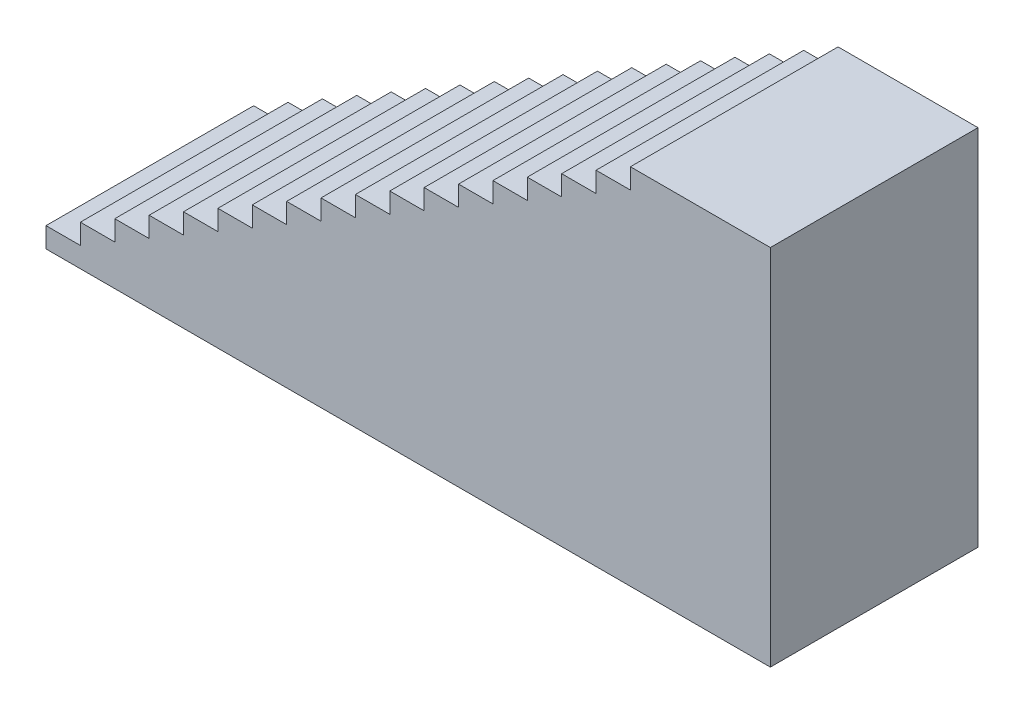
SolidWorks part; units mm, degrees
ref_plane "Front Plane" through (0, 0, 0) normal (0, 0, 1) x (1, 0, 0)
ref_plane "Top Plane" through (0, 0, 0) normal (0, 1, 0) x (1, 0, 0)
ref_plane "Right Plane" through (0, 0, 0) normal (1, 0, 0) x (0, 0, -1)
sketch "Sketch1" plane through (0, 0, 0) normal (0, 0, 1) x (1, 0, 0)
  line L1 (-855.5229, 508.7368) -> (815.0351, 508.7368)
  line L2 (-855.5229, 508.7368) -> (-855.5229, -291.3632)
  line L3 (-855.5229, -291.3632) -> (815.0351, -291.3632)
  line L4 (815.0351, 508.7368) -> (815.0351, -291.3632)
  dimension "D1" = 1670.558
  dimension "D2" = 800.1
extrude "Boss-Extrude1" add sketch "Sketch1" along normal blind 457.2
sketch "Sketch2" plane through (0, 0, 457.2) normal (0, 0, 1) x (1, 0, 0)
  line L0 (815.0351, -291.3632) -> (815.0351, 508.7368) construction
  line L3 (815.0351, 508.7368) -> (-855.5229, 508.7368) construction
  line L4 (506.9331, 508.7368) -> (506.9331, 464.2868)
  line L5 (506.9331, 464.2868) -> (431.2411, 464.2868)
  line L6 (431.2411, 464.2868) -> (431.2411, 419.8368)
  line L7 (431.2411, 419.8368) -> (355.5491, 419.8368)
  line L8 (355.5491, 419.8368) -> (355.5491, 375.3868)
  line L9 (355.5491, 375.3868) -> (279.8571, 375.3868)
  line L10 (279.8571, 375.3868) -> (279.8571, 330.9368)
  line L11 (279.8571, 330.9368) -> (204.1651, 330.9368)
  line L12 (204.1651, 330.9368) -> (204.1651, 286.4868)
  line L13 (204.1651, 286.4868) -> (128.4731, 286.4868)
  line L14 (128.4731, 286.4868) -> (128.4731, 242.0368)
  line L15 (128.4731, 242.0368) -> (52.7811, 242.0368)
  line L16 (52.7811, 242.0368) -> (52.7811, 197.5868)
  line L17 (52.7811, 197.5868) -> (-22.9109, 197.5868)
  line L18 (-22.9109, 197.5868) -> (-22.9109, 153.1368)
  line L19 (-22.9109, 153.1368) -> (-98.6029, 153.1368)
  line L20 (-98.6029, 153.1368) -> (-98.6029, 108.6868)
  line L21 (-98.6029, 108.6868) -> (-174.2949, 108.6868)
  line L22 (-174.2949, 108.6868) -> (-174.2949, 64.2368)
  line L23 (-174.2949, 64.2368) -> (-249.9869, 64.2368)
  line L24 (-249.9869, 64.2368) -> (-249.9869, 19.7868)
  line L25 (-249.9869, 19.7868) -> (-325.6789, 19.7868)
  line L26 (-325.6789, 19.7868) -> (-325.6789, -24.6632)
  line L27 (-325.6789, -24.6632) -> (-401.3709, -24.6632)
  line L28 (-401.3709, -24.6632) -> (-401.3709, -69.1132)
  line L29 (-401.3709, -69.1132) -> (-477.0629, -69.1132)
  line L30 (-477.0629, -69.1132) -> (-477.0629, -113.5632)
  line L31 (-477.0629, -113.5632) -> (-552.7549, -113.5632)
  line L32 (-552.7549, -113.5632) -> (-552.7549, -158.0132)
  line L33 (-552.7549, -158.0132) -> (-628.4469, -158.0132)
  line L34 (-628.4469, -158.0132) -> (-628.4469, -202.4632)
  line L35 (-628.4469, -202.4632) -> (-704.1389, -202.4632)
  line L36 (-704.1389, -202.4632) -> (-704.1389, -246.9132)
  line L37 (-704.1389, -246.9132) -> (-779.8309, -246.9132)
  line L38 (-779.8309, -246.9132) -> (-779.8309, -291.3632)
  line L39 (-779.8309, -291.3632) -> (-855.5229, -291.3632)
  line L40 (-855.5229, -291.3632) -> (-855.5229, 508.7368)
  line L41 (-855.5229, 508.7368) -> (506.9331, 508.7368)
  dimension "D3" = 75.692
  dimension "D4" = 75.692
  dimension "D5" = 75.692
  dimension "D6" = 44.45
  dimension "D7" = 44.45
  dimension "D8" = 75.692
  dimension "D9" = 44.45
  dimension "D10" = 44.45
  dimension "D11" = 44.45
  dimension "D12" = 75.692
  dimension "D13" = 75.692
  dimension "D14" = 75.692
  dimension "D15" = 75.692
  dimension "D16" = 75.692
  dimension "D17" = 75.692
  dimension "D18" = 75.692
  dimension "D19" = 75.692
  dimension "D20" = 75.692
  dimension "D21" = 75.692
  dimension "D22" = 75.692
  dimension "D23" = 75.692
  dimension "D24" = 75.692
  dimension "D25" = 44.45
  dimension "D26" = 44.45
  dimension "D27" = 44.45
  dimension "D28" = 44.45
  dimension "D29" = 44.45
  dimension "D30" = 44.45
  dimension "D31" = 44.45
  dimension "D32" = 44.45
  dimension "D33" = 44.45
  dimension "D34" = 44.45
  dimension "D35" = 44.45
  dimension "D36" = 44.45
  dimension "D37" = 308.102
extrude "Cut-Extrude1" cut sketch "Sketch2" against normal blind 457.2 contours L27 L28 L29 L30 L31 L32 L33 L34 L35 L36 L37 L38 L39 L40 L41 L4 L5 L6 L7 L8 L9 L10 L11 L12 L13 L14 L15 L16 L17 L18 L19 L20 L21 L22 L23 L24 L25 L26
